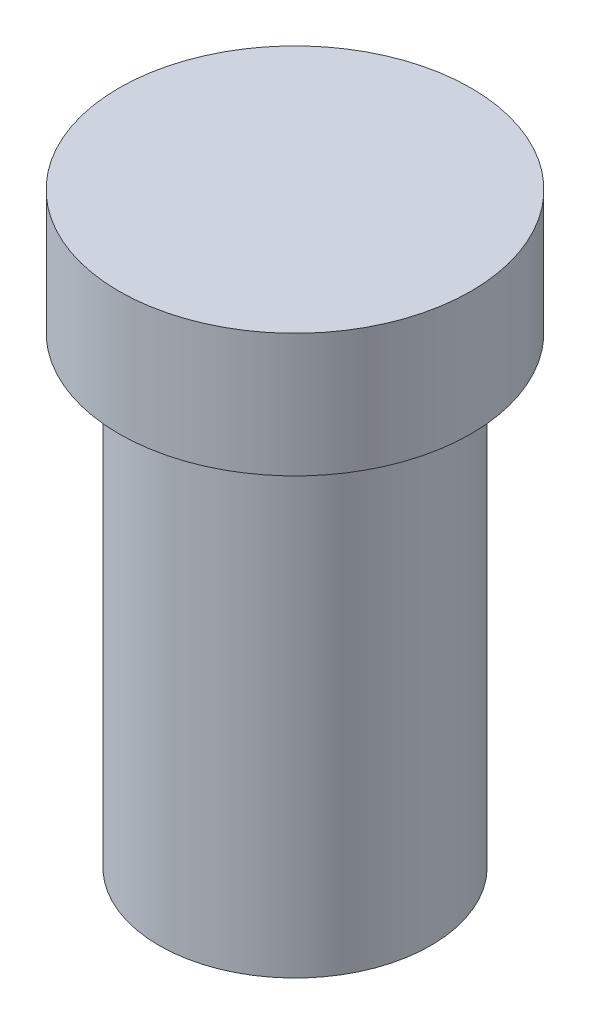
SolidWorks part; units mm, degrees
ref_plane "Front Plane" through (0, 0, 0) normal (0, 0, 1) x (1, 0, 0)
ref_plane "Top Plane" through (0, 0, 0) normal (0, 1, 0) x (1, 0, 0)
ref_plane "Right Plane" through (0, 0, 0) normal (1, 0, 0) x (0, 0, -1)
sketch "Sketch1" plane through (0, 0, 0) normal (0, 1, 0) x (1, 0, 0)
  circle A0 centre (0, 0) radius 22
  dimension "D1" = 44
extrude "Boss-Extrude1" add sketch "Sketch1" along normal blind 75
sketch "Sketch2" plane through (0, 75, 0) normal (0, 1, 0) x (1, 0, 0)
  circle A0 centre (0, 0) radius 28.5
  dimension "D1" = 57
extrude "Boss-Extrude2" add sketch "Sketch2" along normal blind 20
